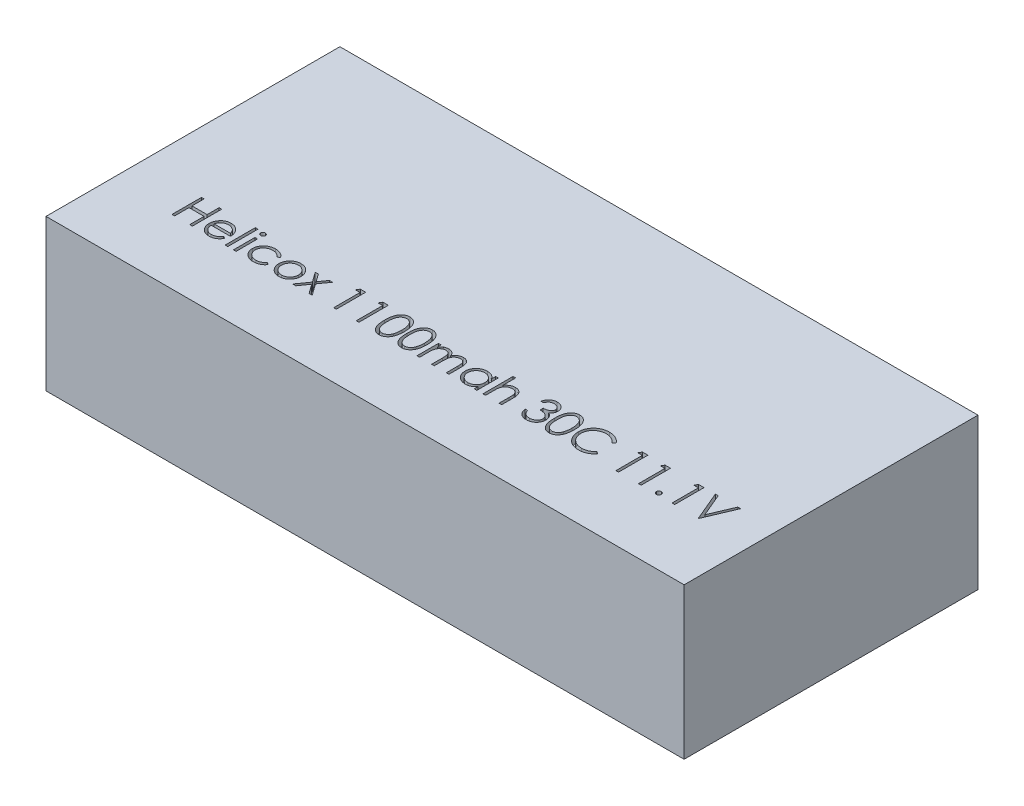
SolidWorks part; units mm, degrees
ref_plane "Front Plane" through (0, 0, 0) normal (0, 0, 1) x (1, 0, 0)
ref_plane "Top Plane" through (0, 0, 0) normal (0, 1, 0) x (1, 0, 0)
ref_plane "Right Plane" through (0, 0, 0) normal (1, 0, 0) x (0, 0, -1)
sketch "Sketch1" plane through (0, 0, 0) normal (0, 1, 0) x (1, 0, 0)
  line L1 (-38, 17.5) -> (38, 17.5)
  line L2 (-38, 17.5) -> (-38, -17.5)
  line L3 (-38, -17.5) -> (38, -17.5)
  line L4 (38, 17.5) -> (38, -17.5)
  line L5 (-38, 17.5) -> (38, -17.5) construction
  line L6 (-38, -17.5) -> (38, 17.5) construction
  point P0 (0, 0)
  dimension "D1" = 76
  dimension "D2" = 35
extrude "Boss-Extrude1" add sketch "Sketch1" along normal blind 18
sketch "Sketch2" plane through (0, 18, 0) normal (0, 1, 0) x (1, 0, 0)
  text T0 "Helicox 1100mah 30C 11.1V"
extrude "Cut-Extrude1" cut sketch "Sketch2" against normal blind 1
